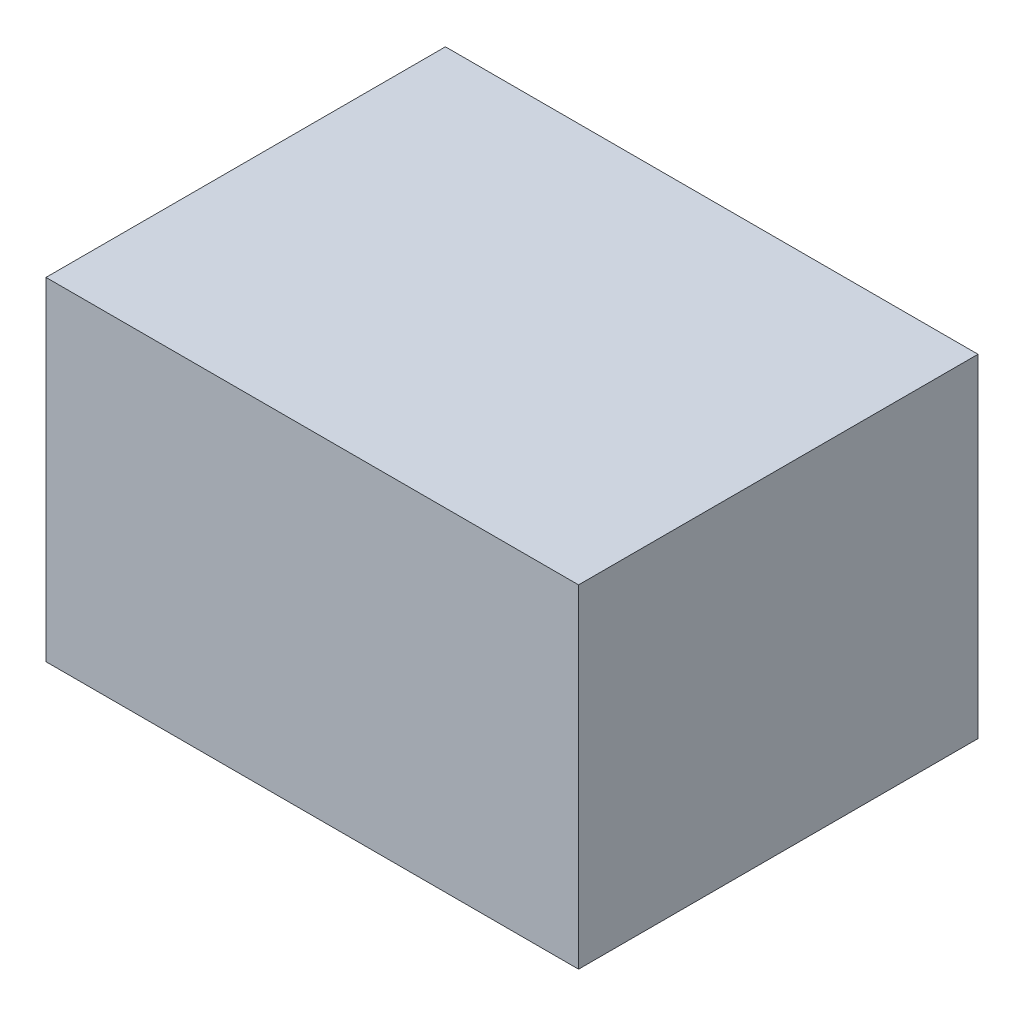
SolidWorks part; units mm, degrees
ref_plane "Front Plane" through (0, 0, 0) normal (0, 0, 1) x (1, 0, 0)
ref_plane "Top Plane" through (0, 0, 0) normal (0, 1, 0) x (1, 0, 0)
ref_plane "Right Plane" through (0, 0, 0) normal (1, 0, 0) x (0, 0, -1)
sketch "Sketch1" plane through (0, 0, 0) normal (0, 1, 0) x (1, 0, 0)
  line L0 (0, 0) -> (800, 0)
  line L1 (0, 0) -> (0, 600)
  line L2 (800, 0) -> (800, 600)
  line L3 (0, 600) -> (800, 600)
  dimension "D1" = 800
  dimension "D2" = 600
extrude "Boss-Extrude1" add sketch "Sketch1" along normal blind 500
